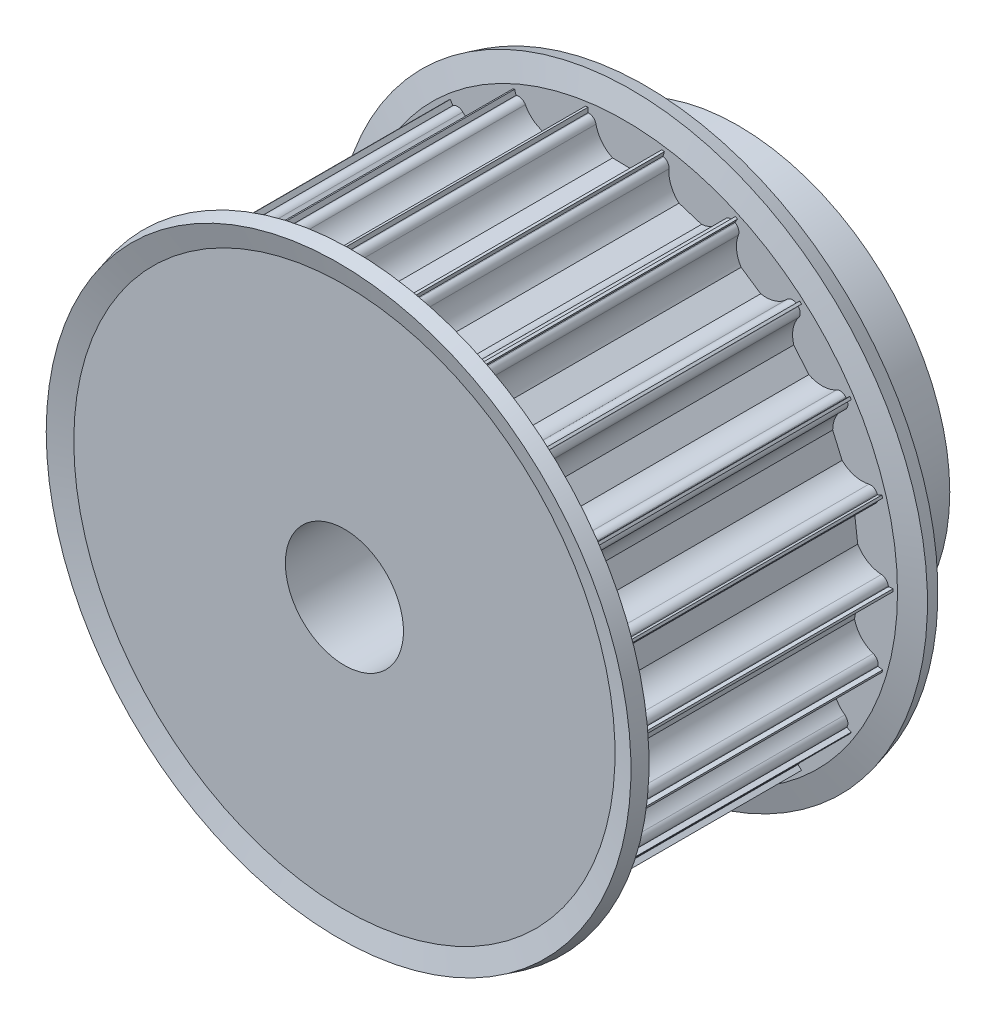
SolidWorks part; units mm, degrees
ref_plane "Front Plane" through (0, 0, 0) normal (0, 0, 1) x (1, 0, 0)
ref_plane "Top Plane" through (0, 0, 0) normal (0, 1, 0) x (1, 0, 0)
ref_plane "Right Plane" through (0, 0, 0) normal (1, 0, 0) x (0, 0, -1)
ref_axis "Axis1" through (0, 0, -88.99) along (0, 0, 1)
sketch "Sketch2" plane through (0, 0, 0) normal (1, 0, 0) x (0, 0, -1)
  line L0 (0, 6) -> (0, 27.25)
  line L1 (0, 27.25) -> (30, 27.25)
  line L2 (30, 27.25) -> (30, 21.5)
  line L3 (30, 21.5) -> (40, 21.5)
  line L4 (40, 21.5) -> (40, 6)
  line L5 (40, 6) -> (0, 6)
  dimension "D1" = 6
  dimension "D2" = 21.25
  dimension "D3" = 30
  dimension "D4" = 10
  dimension "D5" = 15.5
revolve "Revolve1" add sketch "Sketch2" angle 360 about axis through (0, 0, -88.99) along (0, 0, 1)
sketch "Sketch3" plane through (0, 0, 0) normal (0, 0, 1) x (1, 0, 0)
  line L0 (3.6742, 26.5) -> (3.75, 26.5)
  line L1 (-3.75, 26.5) -> (-3.6742, 26.5)
  line L2 (-3.75, 26.5) -> (-3.75, 28.5)
  line L3 (-3.75, 28.5) -> (3.75, 28.5)
  line L4 (3.75, 26.5) -> (3.75, 28.5)
  line L5 (-1.2532, 23.7743) -> (1.1442, 23.7268)
  arc A0 (-2.9394, 25.9) -> (-1.2532, 23.7743) centre (0, 26.5) ccw
  arc A1 (-2.9394, 25.9) -> (-3.6742, 26.5) centre (-3.6742, 25.75) ccw
  arc A2 (2.9394, 25.9) -> (3.6742, 26.5) centre (3.6742, 25.75) cw
  arc A3 (1.1442, 23.7268) -> (2.9394, 25.9) centre (0, 26.5) ccw
  dimension "D4" = 3
  dimension "D5" = 0.75
  dimension "D1" = 26.5
  dimension "D2" = 7.5
  dimension "D3" = 2
  dimension "D6" = 2.75
extrude "Cut-Extrude1" cut sketch "Sketch3" against normal through all
pattern_circular "CirPattern1" count 22 over 360 about axis through (0, 0, 0) along (0, 0, 1) of "Cut-Extrude1"
sketch "Sketch4" plane through (0, 0, 0) normal (1, 0, 0) x (0, 0, -1)
  line L0 (0, 25.679) -> (0, 23.1644) construction
  line L1 (0, 22.6907) -> (1.5, 22.6907)
  line L2 (0, 22.6907) -> (0, 27.4933)
  line L4 (1.5, 22.6907) -> (1.5, 27.6907)
  line L6 (1.5, 27.6907) -> (0.8569, 30.0907)
  line L7 (0, 27.4933) -> (-0.592, 29.7025)
  line L8 (0.8569, 30.0907) -> (-0.592, 29.7025)
  line L10 (15, 26.9539) -> (15, -32.1497) construction
  line L11 (30, 26.9539) -> (0, 26.9539) construction
  line L12 (29.1431, 30.0907) -> (30.592, 29.7025)
  line L13 (30, 27.4933) -> (30.592, 29.7025)
  line L14 (28.5, 27.6907) -> (29.1431, 30.0907)
  line L15 (28.5, 22.6907) -> (28.5, 27.6907)
  line L16 (30, 22.6907) -> (30, 27.4933)
  line L17 (30, 22.6907) -> (28.5, 22.6907)
  dimension "D1" = 5
  dimension "D3" = 1.5
  dimension "D4" = 165
  dimension "D5" = 2.4
revolve "Revolve2" add sketch "Sketch4" angle 360 about axis through (0, 0, -88.99) along (0, 0, 1)
